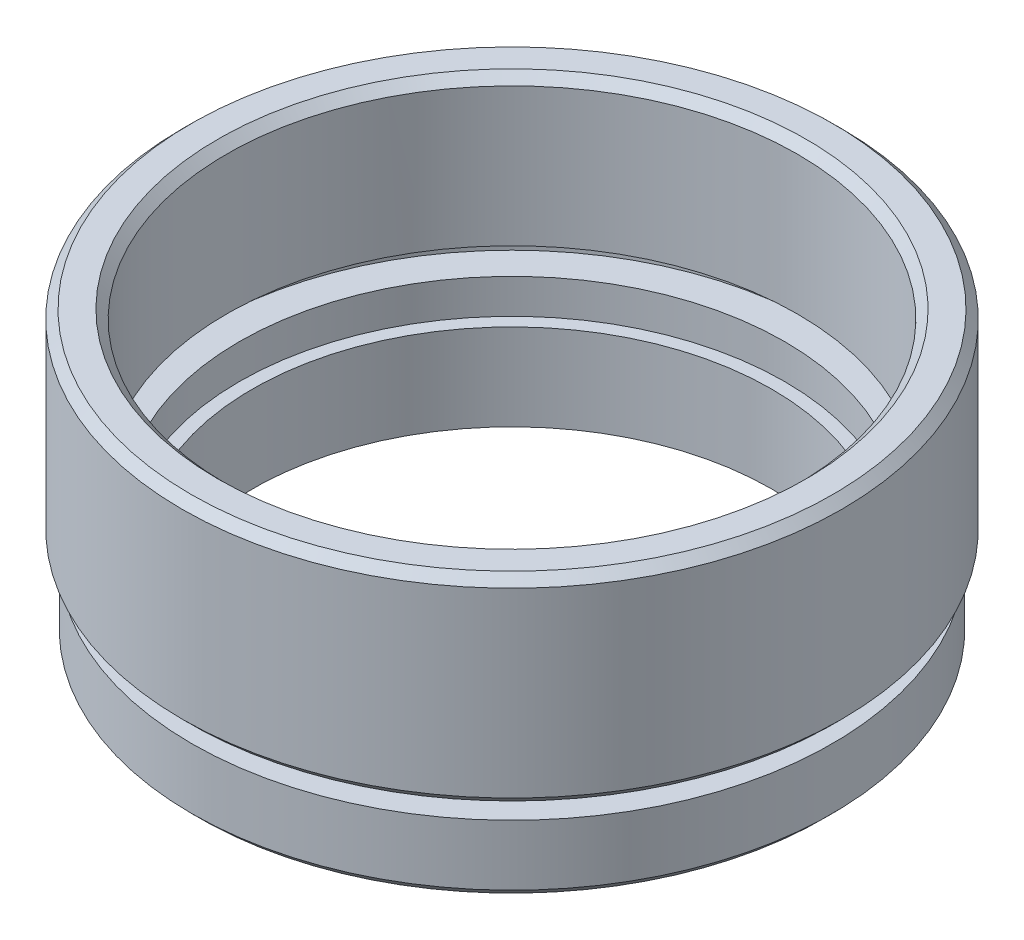
SolidWorks part; units mm, degrees
ref_plane "前视基准面" through (0, 0, 0) normal (0, 0, 1) x (1, 0, 0)
ref_plane "上视基准面" through (0, 0, 0) normal (0, 1, 0) x (1, 0, 0)
ref_plane "右视基准面" through (0, 0, 0) normal (1, 0, 0) x (0, 0, -1)
sketch "草图1" plane through (0, 0, 0) normal (0, 0, 1) x (1, 0, 0)
  line L0 (0, 0) -> (0, 21.8535) construction
  line L1 (15, 0) -> (18.5, 0)
  line L2 (18.5, 0) -> (18.5, 4)
  line L3 (18.5, 4) -> (17, 4)
  line L4 (17, 4) -> (17, 5)
  line L5 (17, 5) -> (19.05, 5)
  line L6 (19.05, 5) -> (19.05, 16.5)
  line L7 (19.05, 16.5) -> (16.5, 16.5)
  line L8 (16.5, 16.5) -> (16.5, 8)
  line L9 (16.5, 8) -> (17.6, 8)
  line L10 (17.6, 8) -> (17.6, 7)
  line L11 (17.6, 7) -> (15.75, 7)
  line L12 (15.75, 7) -> (15.75, 5)
  line L13 (15.75, 5) -> (15, 5)
  line L14 (15, 0) -> (15, 5)
  dimension "D1" = 16.5
  dimension "D2" = 19.05
  dimension "D3" = 16.5
  dimension "D4" = 15.75
  dimension "D5" = 1
  dimension "D6" = 2
  dimension "D7" = 15
  dimension "D8" = 18.5
  dimension "D9" = 1
  dimension "D10" = 5
  dimension "D11" = 5
  dimension "D12" = 17.6
  dimension "D13" = 17
revolve "旋转1" add sketch "草图1" angle 360 about L0
cosmetic thread "装饰螺纹线11" parameters "D2"=35
cosmetic thread "装饰螺纹线12" parameters "D2"=35
chamfer "倒角1" distance 0.5 angle 45 4 edges at (0, 16.5, -16.5) (0, 16.5, -19.05) (0, 5, -19.05) (0, 0, -18.5)
